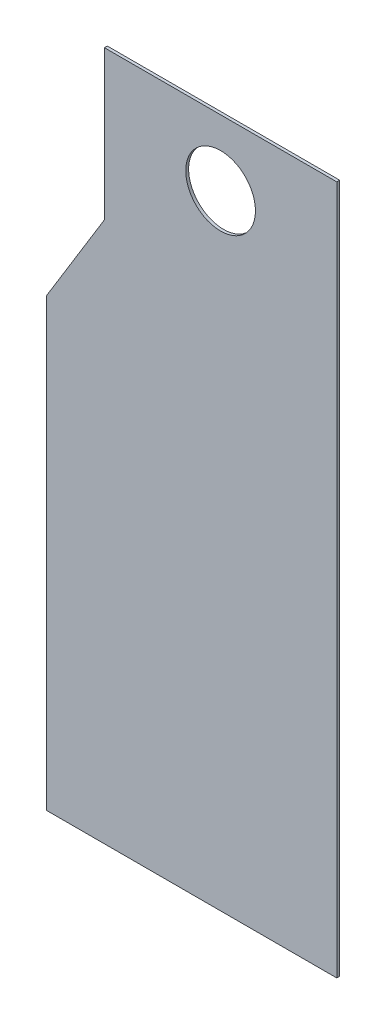
SolidWorks part; units mm, degrees
ref_plane "Front Plane" through (0, 0, 0) normal (0, 0, 1) x (1, 0, 0)
ref_plane "Top Plane" through (0, 0, 0) normal (0, 1, 0) x (1, 0, 0)
ref_plane "Right Plane" through (0, 0, 0) normal (1, 0, 0) x (0, 0, -1)
sketch "Sketch1" plane through (0, 0, 0) normal (0, 0, 1) x (1, 0, 0)
  line L0 (0, 0) -> (0, 154)
  line L1 (0, 154) -> (240, 154)
  line L2 (240, 154) -> (240, -558)
  line L3 (240, -558) -> (-60, -558)
  line L4 (-60, -558) -> (-60, -98)
  line L5 (-60, -98) -> (0, 0)
  circle A0 centre (120, 86) radius 36
  point P5 (120, 154)
  point P8 (0, 86)
  dimension "D7" = 72
  dimension "D1" = 712
  dimension "D2" = 460
  dimension "D3" = 154
  dimension "D4" = 240
  dimension "D5" = 300
  dimension "D6" = 68
extrude "Boss-Extrude1" add sketch "Sketch1" along normal blind 3
